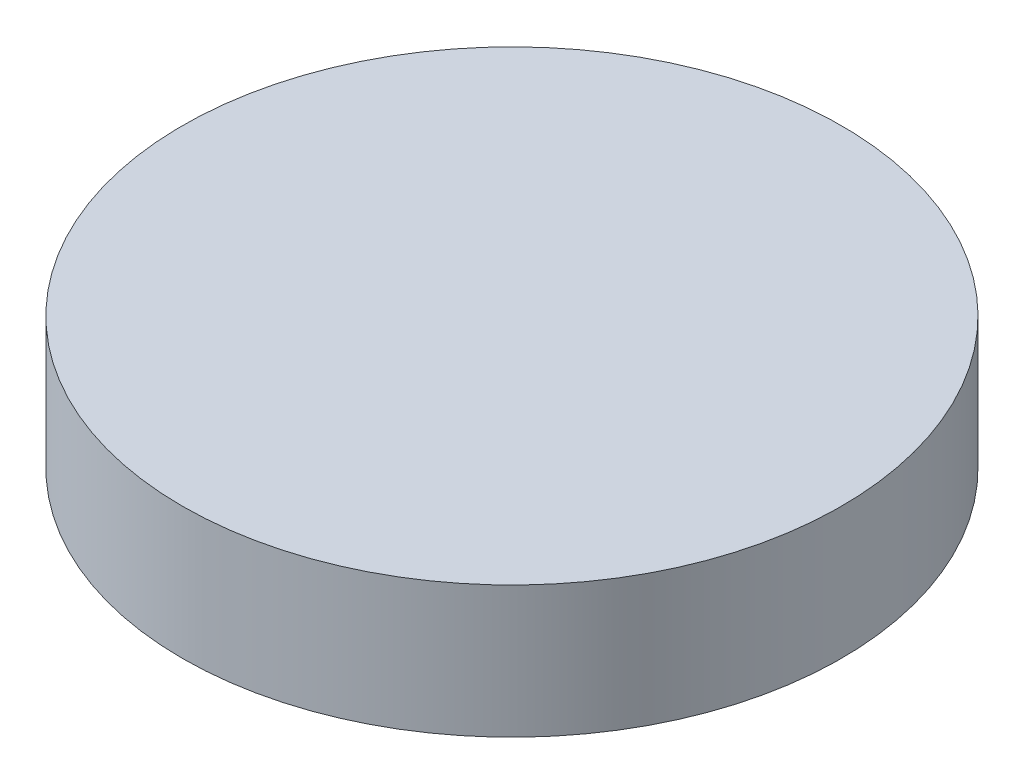
SolidWorks part; units mm, degrees
ref_plane "Front Plane" through (0, 0, 0) normal (0, 0, 1) x (1, 0, 0)
ref_plane "Top Plane" through (0, 0, 0) normal (0, 1, 0) x (1, 0, 0)
ref_plane "Right Plane" through (0, 0, 0) normal (1, 0, 0) x (0, 0, -1)
sketch "Sketch1" plane through (0, 0, 0) normal (0, 1, 0) x (1, 0, 0)
  circle A0 centre (0, 0) radius 127
  dimension "D1" = 254
extrude "Boss-Extrude1" add sketch "Sketch1" along normal blind 50.8
